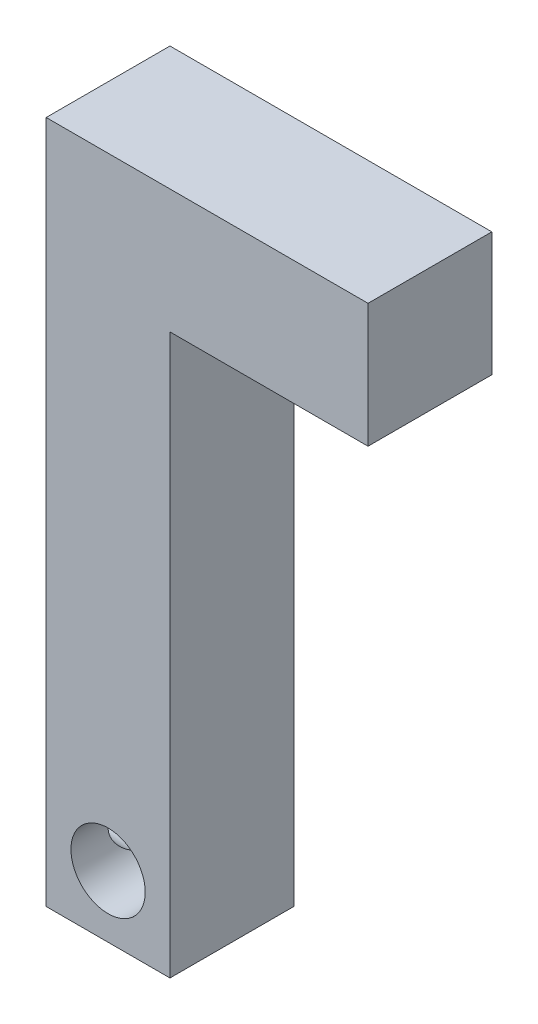
SolidWorks part; units mm, degrees
other "DetailItem1" parameters "D2"=6.1604, "D1"=3.8755, "D3"=2.907
other "DetailItem2"
ref_plane "Front Plane" through (0, 0, 0) normal (0, 0, 1) x (1, 0, 0)
ref_plane "Top Plane" through (0, 0, 0) normal (0, 1, 0) x (1, 0, 0)
ref_plane "Right Plane" through (0, 0, 0) normal (1, 0, 0) x (0, 0, -1)
sketch "Sketch1" plane through (0, 0, 0) normal (0, 0, 1) x (1, 0, 0)
  line L9 (0, 0) -> (6.35, 0)
  line L10 (0, 0) -> (0, -35.052)
  line L11 (0, -35.052) -> (6.35, -35.052)
  line L12 (6.35, 0) -> (6.35, -35.052)
  line L13 (0, 0) -> (16.51, 0)
  line L14 (0, 0) -> (0, -6.35)
  line L15 (0, -6.35) -> (16.51, -6.35)
  line L16 (16.51, 0) -> (16.51, -6.35)
  dimension "D1" = 16.51
  dimension "D2" = 35.052
  dimension "D3" = 6.35
  dimension "D4" = 6.35
extrude "Boss-Extrude1" add sketch "Sketch1" along normal blind 6.35 contours L16 L13 L12 L15
sketch "Sketch2" plane through (0, 0, 6.35) normal (0, 0, 1) x (1, 0, 0)
  line L0 (0, 0) -> (0, -35.052) construction
  line L1 (0, -35.052) -> (6.35, -35.052) construction
  circle A0 centre (3.175, -31.877) radius 1.905
  dimension "D3" = 3.81
  dimension "D1" = 3.175
  dimension "D2" = 3.175
extrude "Cut-Extrude1" cut sketch "Sketch2" against normal through all
sketch "Sketch3" plane through (0, 0, 0) normal (-1, 0, 0) x (0, 0, 1)
  line L0 (6.35, -35.052) -> (0, -35.052) construction
  line L1 (0, 0) -> (0, -35.052) construction
  circle A1 centre (3.175, -31.877) radius 1.27
extrude "Cut-Extrude2" cut sketch "Sketch3" against normal up to next
